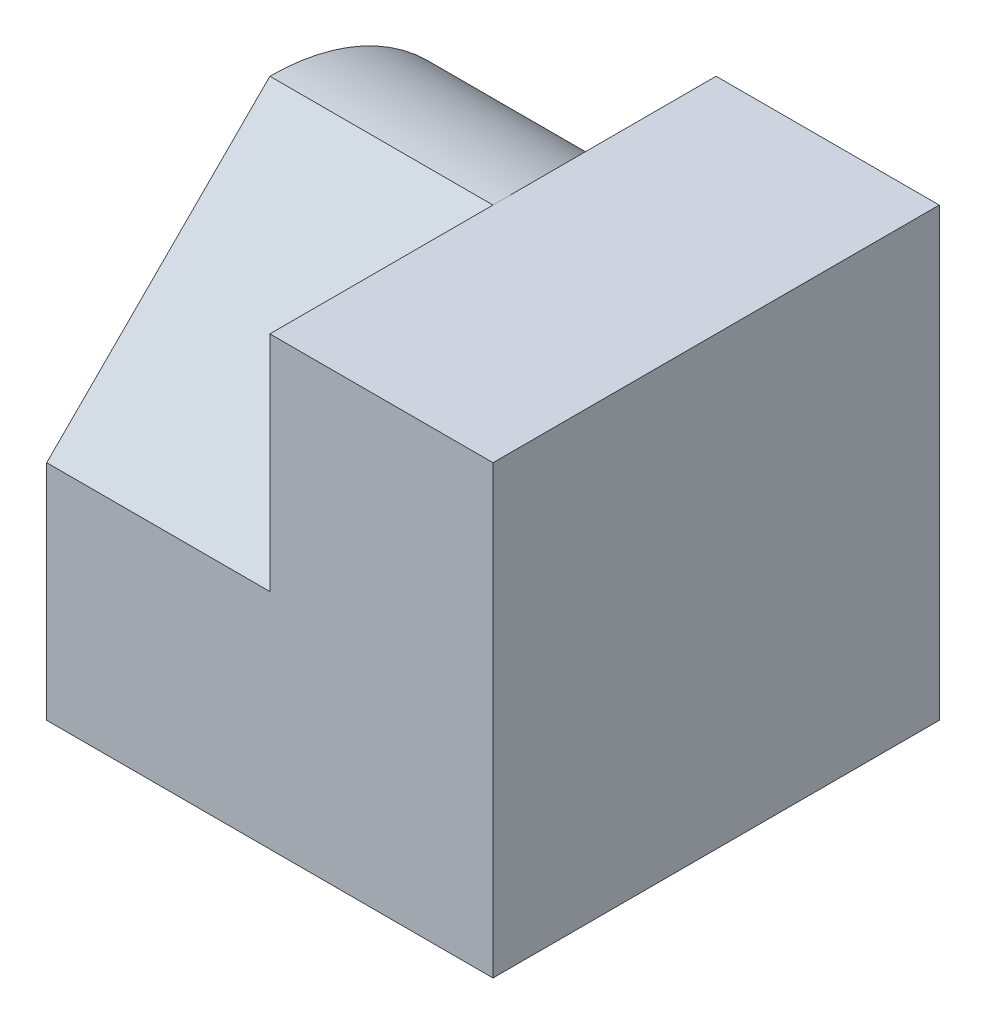
SolidWorks part; units mm, degrees
ref_plane "Front" through (0, 0, 0) normal (0, 0, 1) x (1, 0, 0)
ref_plane "Top" through (0, 0, 0) normal (0, 1, 0) x (1, 0, 0)
ref_plane "Right" through (0, 0, 0) normal (1, 0, 0) x (0, 0, -1)
sketch "Sketch1" plane through (0, 0, 0) normal (0, 1, 0) x (1, 0, 0)
  line L1 (-2, -2) -> (2, -2)
  line L2 (-2, -2) -> (-2, 2)
  line L3 (-2, 2) -> (2, 2)
  line L4 (2, -2) -> (2, 2)
  line L5 (-2, -2) -> (2, 2) construction
  line L6 (-2, 2) -> (2, -2) construction
  point P0 (0, 0)
  dimension "D1" = 4
  dimension "D2" = 4
extrude "Boss-Extrude1" add sketch "Sketch1" along normal blind 4
sketch "Sketch2" plane through (-2, 0, 0) normal (-1, 0, 0) x (0, 0, 1)
  line L0 (2, 2) -> (0, 4)
  line L1 (2, 4) -> (2, 0) construction
  line L2 (-2, 4) -> (2, 4) construction
  line L9 (-2, 0) -> (2, 0)
  line L10 (2, 0) -> (2, 4)
  line L11 (2, 4) -> (-2, 4)
  line L12 (-2, 4) -> (-2, 0)
  line L13 (-2, 0) -> (2, 0)
  line L14 (2, 0) -> (2, 4)
  line L15 (2, 4) -> (-2, 4)
  line L16 (-2, 4) -> (-2, 0)
  arc A0 (-2, 2) -> (0, 4) centre (0, 2) cw
  dimension "D1" = 0
extrude "Cut-Extrude1" cut sketch "Sketch2" against normal blind 2
